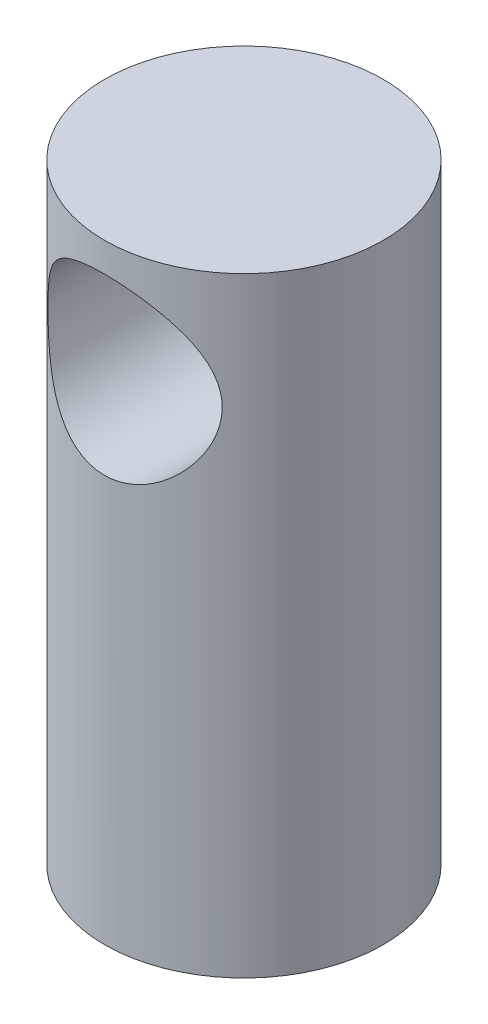
SolidWorks part; units mm, degrees
material "PE Low Density Film"
ref_plane "Front Plane" through (0, 0, 0) normal (0, 0, 1) x (1, 0, 0)
ref_plane "Top Plane" through (0, 0, 0) normal (0, 1, 0) x (1, 0, 0)
ref_plane "Right Plane" through (0, 0, 0) normal (1, 0, 0) x (0, 0, -1)
sketch "Sketch1" plane through (0, 0, 0) normal (0, 1, 0) x (1, 0, 0)
  circle A0 centre (0, 0) radius 8
  dimension "D1" = 16
extrude "Boss-Extrude2" add sketch "Sketch1" along normal blind 35
sketch "Sketch3" plane through (0, 0, 0) normal (0, 0, 1) x (1, 0, 0)
  circle A0 centre (0, 28.3221) radius 5
extrude "Cut-Extrude2" cut sketch "Sketch3" against normal through all both and the other way through all
